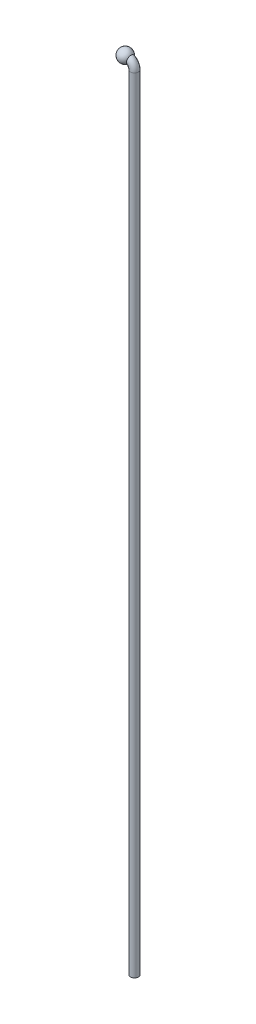
SolidWorks part; units mm, degrees
ref_plane "Front Plane" through (0, 0, 0) normal (0, 0, 1) x (1, 0, 0)
ref_plane "Top Plane" through (0, 0, 0) normal (0, 1, 0) x (1, 0, 0)
ref_plane "Right Plane" through (0, 0, 0) normal (1, 0, 0) x (0, 0, -1)
sketch "Sketch1" plane through (0, 0, 0) normal (1, 0, 0) x (0, 0, -1)
  line L0 (0, 0.165) -> (0, -0.165) construction
  circle A0 centre (0, 0) radius 0.15
  dimension "D1" = 0.3
sketch "Sketch3" plane through (0, 0, 0) normal (0, 0, 1) x (1, 0, 0)
  line L0 (0, 0) -> (0.05, 0)
  line L1 (0.35, -0.3) -> (0.35, -30)
  arc A0 (0.35, -0.3) -> (0.05, 0) centre (0.05, -0.3) ccw
  point P6 (0.35, 0)
  dimension "D3" = 0.3
  dimension "D1" = 30
  dimension "D2" = 0.35
sweep "Sweep1" add profiles "Sketch1" path "Sketch3"
sketch "Sketch6" plane through (0, 0, 0) normal (-1, 0, 0) x (0, 0, 1)
  circle A0 centre (0, 0) radius 0.2
  dimension "D1" = 0.4
extrude "Boss-Extrude1" add sketch "Sketch6" against normal blind 0.15
sketch "Sketch4" plane through (0, 0, 0) normal (-1, 0, 0) x (0, 0, 1)
  line L0 (0, 0.25) -> (0, -0.25)
  arc A0 (0, 0.25) -> (0, -0.25) centre (0, 0) ccw
  circle A1 centre (0, 0) radius 0.2 construction
  dimension "D1" = 0.5
revolve "Revolve2" add sketch "Sketch4" angle 360 about L0
sketch "Sketch5" plane through (0, 0, 0) normal (0, 0, 1) x (1, 0, 0)
  line L0 (0.35, -0.3) -> (0.35, -30) construction
  line L1 (0.35, -0.3) -> (0.35, -30)
